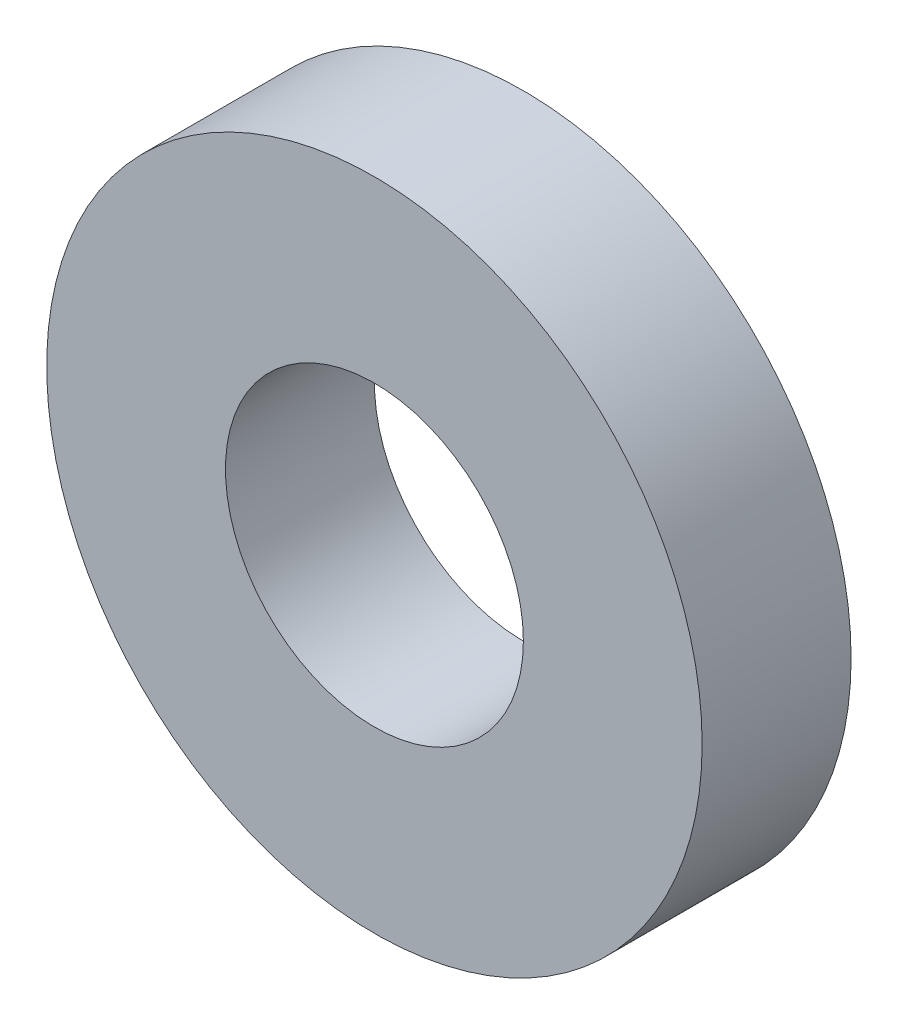
SolidWorks part; units mm, degrees
ref_plane "Front Plane" through (0, 0, 0) normal (0, 0, 1) x (1, 0, 0)
ref_plane "Top Plane" through (0, 0, 0) normal (0, 1, 0) x (1, 0, 0)
ref_plane "Right Plane" through (0, 0, 0) normal (1, 0, 0) x (0, 0, -1)
sketch "Sketch1" plane through (0, 0, 0) normal (0, 0, 1) x (1, 0, 0)
  circle A0 centre (0, 0) radius 6
  circle A1 centre (0, 0) radius 13.2
extrude "Boss-Extrude1" add sketch "Sketch1" along normal blind 6
sketch "Sketch2" plane through (0, 0, 6) normal (0, 0, 1) x (1, 0, 0)
  line L0 (0, 0) -> (0, 15.2) construction
  line L1 (-1.8199, 15.2) -> (0, 0) construction
  line L2 (1.8199, 15.2) -> (0, 0) construction
  line L3 (-1122.4778, 12) -> (1122.4778, 12)
  arc A0 (-1.8199, 15.2) -> (-9.5054, 12) centre (0, 0) ccw
